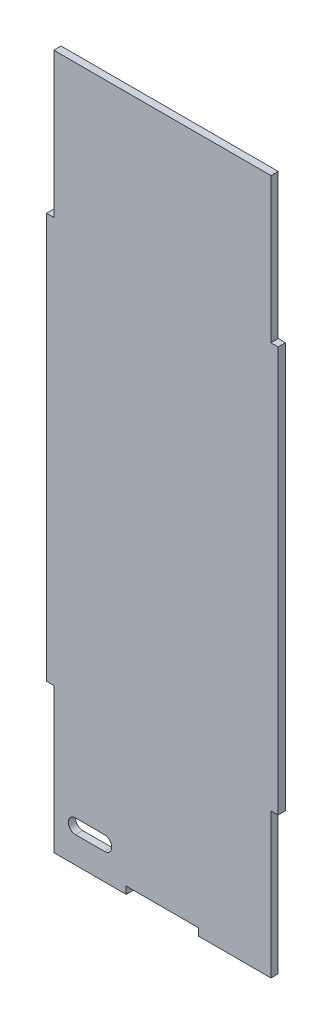
SolidWorks part; units mm, degrees
ref_plane "Front Plane" through (0, 0, 0) normal (0, 0, 1) x (1, 0, 0)
ref_plane "Top Plane" through (0, 0, 0) normal (0, 1, 0) x (1, 0, 0)
ref_plane "Right Plane" through (0, 0, 0) normal (1, 0, 0) x (0, 0, -1)
sketch "Sketch1" plane through (0, 0, 0) normal (0, 0, 1) x (1, 0, 0)
  line L1 (0, 0) -> (-228.6, 0)
  line L2 (0, 0) -> (0, 609.6)
  line L3 (0, 609.6) -> (-228.6, 609.6)
  line L4 (-228.6, 0) -> (-228.6, 609.6)
  dimension "D1" = 228.6
  dimension "D2" = 609.6
extrude "Boss-Extrude1" add sketch "Sketch1" along normal blind 6.35
sketch "Sketch2" plane through (0, 0, 6.35) normal (0, 0, 1) x (1, 0, 0)
  line L0 (-165.0954, 29.4853) -> (-190.4954, 29.4853) construction
  line L1 (-165.0954, 23.1353) -> (-190.4954, 23.1353)
  line L2 (-165.0954, 35.8353) -> (-190.4954, 35.8353)
  arc A0 (-165.0954, 23.1353) -> (-165.0954, 35.8353) centre (-165.0954, 29.4853) ccw
  arc A1 (-190.4954, 35.8353) -> (-190.4954, 23.1353) centre (-190.4954, 29.4853) ccw
  point P2 (-177.7954, 29.4853)
extrude "Cut-Extrude1" cut sketch "Sketch2" against normal blind 6.35
sketch "Sketch5" plane through (0, 0, 6.35) normal (0, 0, 1) x (1, 0, 0)
  line L0 (-19.05, 609.6) -> (-19.05, 482.6)
  line L1 (0, 609.6) -> (-228.6, 609.6) construction
  line L2 (-19.05, 482.6) -> (0, 482.6)
  line L3 (0, 0) -> (0, 609.6) construction
sketch "Sketch6" plane through (0, 0, 6.35) normal (0, 0, 1) x (1, 0, 0)
  line L0 (-19.05, 0) -> (-19.05, 127)
  line L1 (-228.6, 0) -> (0, 0) construction
  line L2 (-19.05, 127) -> (0, 127)
  line L3 (0, 0) -> (0, 609.6) construction
extrude "Cut-Extrude4" cut sketch "Sketch6" against normal through all and the other way through all flip side to cut
ref_plane "Plane1" through (-19.05, 0, 6.35) normal (1, 0, 0) x (0, 0, -1)
extrude "Cut-Extrude7" cut sketch "Sketch5" against normal through all and the other way through all
ref_plane "Plane2" through (0, 127, 6.35) normal (-1, 0, 0) x (0, 0, 1)
sketch "Sketch11" plane through (0, 0, 6.35) normal (0, 0, 1) x (1, 0, 0)
  line L2 (-12.7, 482.6) -> (-12.7, 127)
  line L3 (0, 482.6) -> (-19.05, 482.6) construction
  line L4 (0, 127) -> (-19.05, 127) construction
extrude "Cut-Extrude8" cut sketch "Sketch11" against normal through all and the other way through all
sketch "Sketch12" plane through (0, 0, 6.35) normal (0, 0, 1) x (1, 0, 0)
  line L1 (-228.6, 609.6) -> (-228.6, 0) construction
  line L3 (-209.55, 609.6) -> (-209.55, 482.6)
  line L4 (-19.05, 609.6) -> (-228.6, 609.6) construction
  line L5 (-209.55, 482.6) -> (-228.6, 482.6)
ref_plane "Plane3" through (-19.05, 609.6, 6.35) normal (-1, 0, 0) x (0, 0, 1)
sketch "Sketch15" plane through (0, 0, 6.35) normal (0, 0, 1) x (1, 0, 0)
  line L1 (-228.6, 609.6) -> (-228.6, 0) construction
  line L2 (-209.55, 0) -> (-209.55, 127)
  line L3 (-228.6, 0) -> (-19.05, 0) construction
  line L4 (-209.55, 127) -> (-228.6, 127)
extrude "Cut-Extrude9" cut sketch "Sketch15" against normal through all and the other way through all
extrude "Cut-Extrude10" cut sketch "Sketch12" against normal through all and the other way through all flip side to cut
sketch "Sketch16" plane through (0, 0, 6.35) normal (0, 0, 1) x (1, 0, 0)
  line L2 (-215.9, 482.6) -> (-215.9, 127)
  line L3 (-228.6, 482.6) -> (-209.55, 482.6) construction
  line L4 (-228.6, 127) -> (-209.55, 127) construction
extrude "Cut-Extrude11" cut sketch "Sketch16" against normal through all and the other way through all flip side to cut
ref_plane "Plane4" through (-209.55, 0, 6.35) normal (1, 0, 0) x (0, 0, -1)
sketch "Sketch18" plane through (0, 0, 6.35) normal (0, 0, 1) x (1, 0, 0)
  line L0 (-82.55, 0) -> (-82.55, 6.35)
  line L1 (-209.55, 0) -> (-19.05, 0) construction
  line L4 (-146.05, 6.35) -> (-146.05, 0)
  line L7 (-146.05, 6.35) -> (-82.55, 6.35)
extrude "Cut-Extrude12" cut sketch "Sketch18" against normal through all and the other way through all
